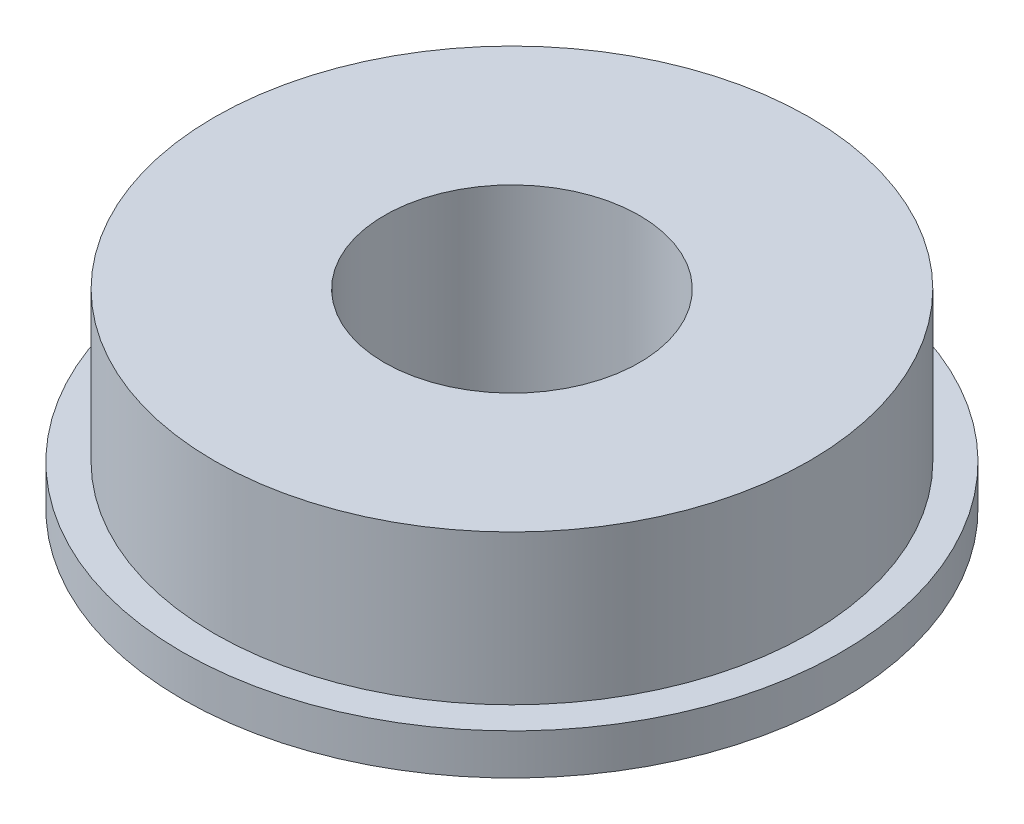
SolidWorks part; units mm, degrees
ref_plane "前基準面" through (0, 0, 0) normal (0, 0, 1) x (1, 0, 0)
ref_plane "上基準面" through (0, 0, 0) normal (0, 1, 0) x (1, 0, 0)
ref_plane "右基準面" through (0, 0, 0) normal (1, 0, 0) x (0, 0, -1)
sketch "草圖1" plane through (0, 0, 0) normal (0, 1, 0) x (1, 0, 0)
  circle A0 centre (0, 0) radius 12.3063
  dimension "D1" = 24.6126
extrude "填料-伸長1" add sketch "草圖1" along normal blind 1.524
sketch "草圖2" plane through (0, 1.524, 0) normal (0, 1, 0) x (1, 0, 0)
  circle A0 centre (0, 0) radius 11.1125
  dimension "D1" = 22.225
extrude "填料-伸長2" add sketch "草圖2" along normal blind 5.588
sketch "草圖3" plane through (0, 7.112, 0) normal (0, 1, 0) x (1, 0, 0)
  circle A0 centre (0, 0) radius 4.7625
  dimension "D1" = 9.525
extrude "除料-伸長1" cut sketch "草圖3" against normal through all
